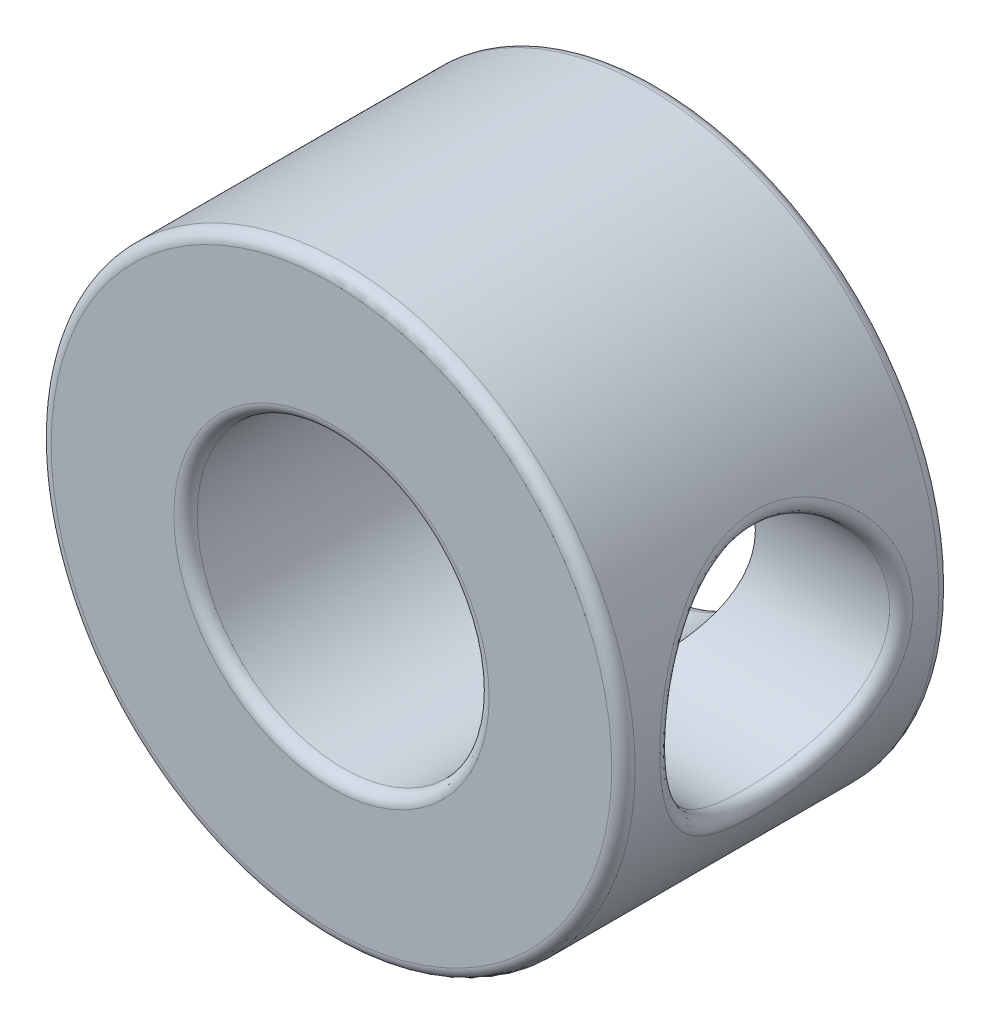
SolidWorks part; units mm, degrees
ref_plane "Front Plane" through (0, 0, 0) normal (0, 0, 1) x (1, 0, 0)
ref_plane "Top Plane" through (0, 0, 0) normal (0, 1, 0) x (1, 0, 0)
ref_plane "Right Plane" through (0, 0, 0) normal (1, 0, 0) x (0, 0, -1)
sketch "Sketch2" plane through (0, 0, 0) normal (0, 0, 1) x (1, 0, 0)
  circle A0 centre (0, 0) radius 6.35
  dimension "D1" = 12.7
extrude "Boss-Extrude1" add sketch "Sketch2" along normal blind 7.112
sketch "Sketch3" plane through (0, 0, 7.112) normal (0, 0, 1) x (1, 0, 0)
  circle A0 centre (0, 0) radius 3.175
  dimension "D1" = 6.35
extrude "Cut-Extrude1" cut sketch "Sketch3" against normal blind 19.05 contours A0
sketch "Sketch4" plane through (0, 0, 0) normal (1, 0, 0) x (0, 0, -1)
  circle A0 centre (-3.5687, 0) radius 2.5
  dimension "D1" = 5
  dimension "D2" = 3.5687
extrude "Cut-Extrude2" cut sketch "Sketch4" along normal blind 19.05
fillet "Fillet1" radius 0.254 5 edges at (3.175, 0, 0) (6.35, 0, 0) (6.3393, 0.3688, 1.096) (3.175, 0, 7.112) (6.35, 0, 7.112)
